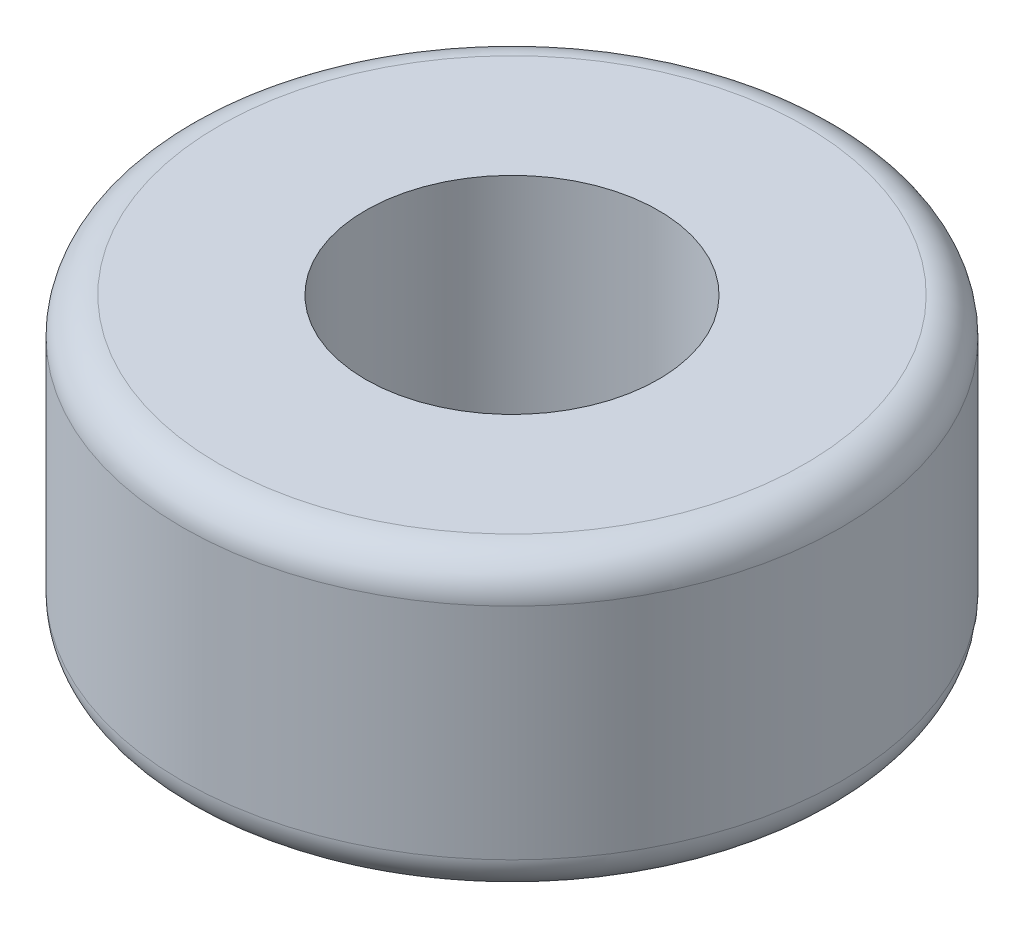
SolidWorks part; units mm, degrees
ref_plane "Front Plane" through (0, 0, 0) normal (0, 0, 1) x (1, 0, 0)
ref_plane "Top Plane" through (0, 0, 0) normal (0, 1, 0) x (1, 0, 0)
ref_plane "Right Plane" through (0, 0, 0) normal (1, 0, 0) x (0, 0, -1)
sketch "Sketch1" plane through (0, 0, 0) normal (0, 1, 0) x (1, 0, 0)
  circle A0 centre (0, 0) radius 4.5
  circle A1 centre (0, 0) radius 2
  dimension "D1" = 4
  dimension "D2" = 9
extrude "Boss-Extrude1" add sketch "Sketch1" along normal blind 4
fillet "Fillet1" radius 0.5 2 edges at (0, 0, 4.5) (0, 4, 4.5)
